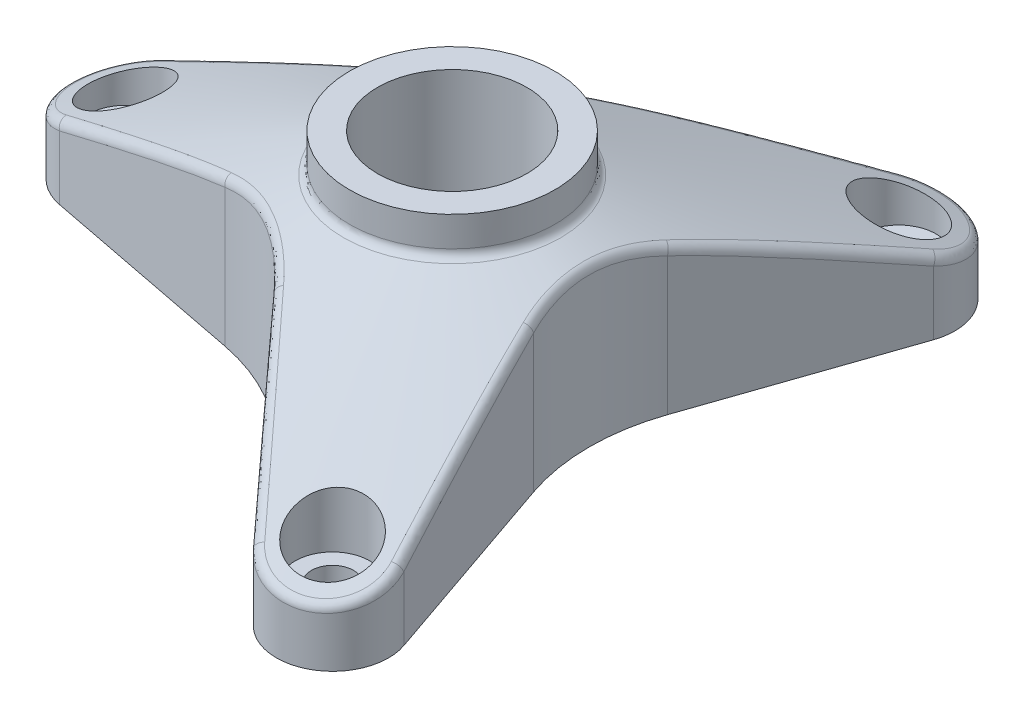
SolidWorks part; units mm, degrees
ref_plane "Front Plane" through (0, 0, 0) normal (0, 0, 1) x (1, 0, 0)
ref_plane "Top Plane" through (0, 0, 0) normal (0, 1, 0) x (1, 0, 0)
ref_plane "Right Plane" through (0, 0, 0) normal (1, 0, 0) x (0, 0, -1)
sketch "Sketch1" plane through (0, 0, 0) normal (0, 1, 0) x (1, 0, 0)
  line L0 (0, 0) -> (-35, 0) construction
  line L1 (0, 0) -> (17.5, -30.3109) construction
  line L2 (0, 0) -> (17.5, 30.3109) construction
  line L3 (-36.1449, 5.8898) -> (-14.1405, 10.167)
  line L4 (-1.7346, 17.3295) -> (12.9717, 34.2472)
  line L5 (-36.1449, -5.8898) -> (-14.1405, -10.167)
  line L6 (-1.7346, -17.3295) -> (12.9717, -34.2472)
  line L7 (23.1731, 28.3575) -> (15.8751, 7.1625)
  line L8 (15.8751, -7.1625) -> (23.1731, -28.3575)
  circle A4 centre (0, 0) radius 35 construction
  arc A5 (-36.1449, 5.8898) -> (-36.1449, -5.8898) centre (-35, 0) ccw
  arc A6 (12.9717, -34.2472) -> (23.1731, -28.3575) centre (17.5, -30.3109) ccw
  arc A7 (23.1731, 28.3575) -> (12.9717, 34.2472) centre (17.5, 30.3109) ccw
  arc A8 (-1.7346, 17.3295) -> (-14.1405, 10.167) centre (-18.3383, 31.7628) cw
  arc A9 (-1.7346, -17.3295) -> (-14.1405, -10.167) centre (-18.3383, -31.7628) ccw
  arc A10 (15.8751, 7.1625) -> (15.8751, -7.1625) centre (36.6765, 0) ccw
  point P16 (0, 0)
  point P18 (0, 0)
  point P19 (0, 0)
  point P20 (0, 0)
  point P21 (0, 0)
  point P22 (0, 0)
  point P23 (-6.1301, 11.724)
  point P24 (0, 0)
  point P25 (14.1197, 0)
  point P26 (0, 0)
  point P29 (-6.7044, 11.6124)
  point P33 (-6.7044, -11.6124)
  point P36 (13.4088, 0)
  dimension "D1" = 70
  dimension "D2" = 120
  dimension "D3" = 120
  dimension "D4" = 12
  dimension "D5" = 12
  dimension "D6" = 12
  dimension "D8" = 22
  dimension "D9" = 22
  dimension "D10" = 22
  dimension "D11" = 22
  dimension "D12" = 22
  dimension "D7" = 22
extrude "Boss-Extrude1" add sketch "Sketch1" along normal blind 22
hole_wizard "CBORE for M4 SHCS1" positions "3DSketch1" profile "Sketch2" counterbore size "M4" standard "ANSI Metric" end condition through all
sketch3d "3DSketch1"
  line L0 (-35, 22, 0) -> (-35, 0, 0) construction
  line L1 (17.5, 22, 30.3109) -> (17.5, 0, 30.3109) construction
  line L2 (17.5, 22, -30.3109) -> (17.5, 0, -30.3109) construction
  point P0 (-35, 22, 0)
  point P4 (17.5, 22, 30.3109)
  point P8 (17.5, 22, -30.3109)
sketch "Sketch2" plane through (-35, 22, 0) normal (1, 0, 0) x (0, 0, 1)
  line L0 (0, 0) -> (0, 22)
  line L1 (0, 22) -> (2.25, 22)
  line L3 (2.25, 22) -> (2.25, 18)
  line L4 (2.25, 18) -> (4, 18)
  line L5 (4, 18) -> (4, 0)
  line L7 (4, 0) -> (0, 0)
  line L11 (0, -6.35) -> (0, 107.95) construction
  dimension "Thru Hole Dia." = 4.5
  dimension "Thru Hole Depth" = 22
  dimension "C'Bore Dia." = 8
  dimension "C'Bore Depth" = 18
sketch "Sketch3" plane through (0, 0, 0) normal (0, 0, 1) x (1, 0, 0)
  line L0 (-41, 25) -> (0, 25) construction
  line L1 (-14.1405, 0) -> (-1.7346, 0) construction
  line L2 (0, 25) -> (0, -10.0163) construction
  line L3 (0, 25) -> (-11, 25) construction
  line L4 (-11, 25) -> (-11, 18.1208)
  line L5 (-11, 18.1208) -> (-41, 6)
  line L6 (-41, 6) -> (-41, 31.8878)
  line L7 (-41, 31.8878) -> (-11, 31.8878)
  line L9 (-41, 0) -> (-36.1449, 0) construction
  line L11 (-11, 25) -> (-11, 31.8878)
  line L12 (-41, 22) -> (-41, 0) construction
  point P13 (-35, 31.8878)
  point P14 (-41, 6)
  dimension "D2" = 25
  dimension "D3" = 0
  dimension "D4" = 112
  dimension "D5" = 11
  dimension "D6" = 6
revolve "Cut-Revolve1" cut sketch "Sketch3" angle 360 about L2
hole_wizard "Ø16.0 (16) Diameter Hole1" positions "3DSketch2" profile "Sketch4" hole size "Ø16.0" standard "ANSI Metric" end condition through all
sketch3d "3DSketch2"
  line L0 (0, 18.1208, 0) -> (0, 22, 0) construction
  point P0 (0, 22, 0)
sketch "Sketch4" plane through (0, 22, 0) normal (1, 0, 0) x (0, 0, 1)
  line L0 (0, 0) -> (0, 22)
  line L1 (0, 22) -> (8, 22)
  line L2 (8, 22) -> (8, 0)
  line L5 (8, 0) -> (0, 0)
  line L11 (0, -6.35) -> (0, 107.95) construction
  dimension "Thru Hole Dia." = 16
  dimension "Thru Hole Depth" = 22
fillet "Fillet4" radius 1 1 edges at (-11, 18.1208, 0)
fillet "Fillet5" radius 1 12 edges at (-8.3446, 16.6054, -12.1636) (-41, 6, -0.0223) (-6.3616, 16.6054, 13.3085) (20.4807, 6, 35.5182) (14.7063, 16.6054, -1.1449) (20.5192, 6, -35.4959)
